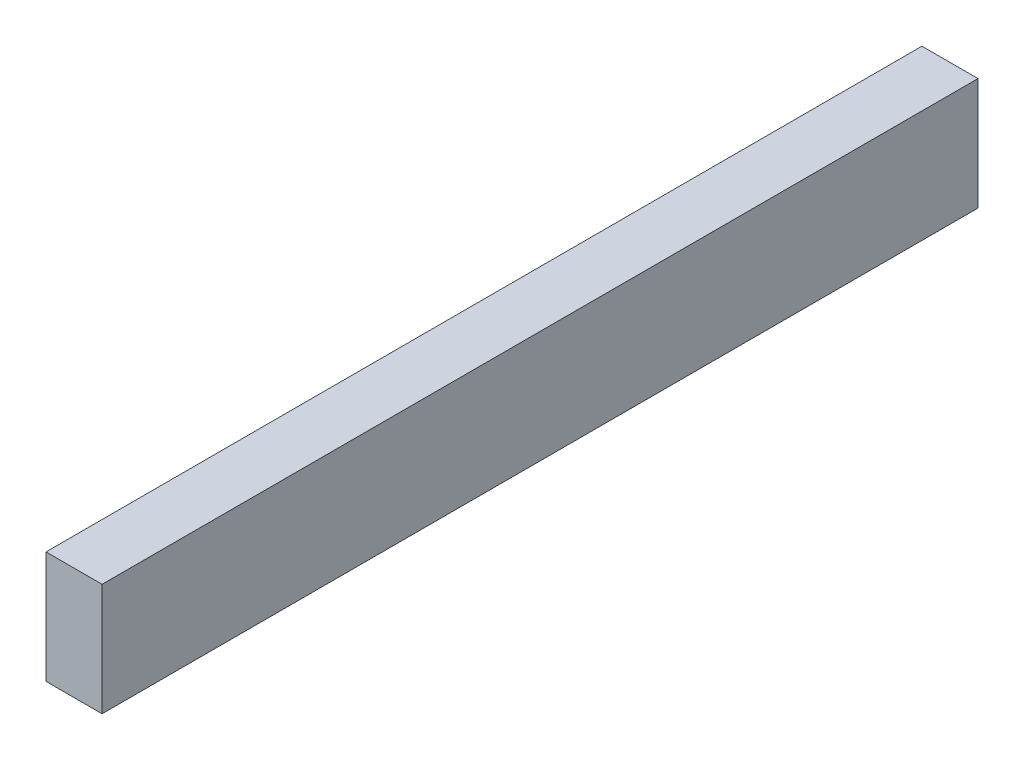
SolidWorks part; units mm, degrees
material "Cedar"
ref_plane "Front Plane" through (0, 0, 0) normal (0, 0, 1) x (1, 0, 0)
ref_plane "Top Plane" through (0, 0, 0) normal (0, 1, 0) x (1, 0, 0)
ref_plane "Right Plane" through (0, 0, 0) normal (1, 0, 0) x (0, 0, -1)
sketch "Sketch1" plane through (0, 0, 0) normal (1, 0, 0) x (0, 0, -1)
  line L1 (-119.1459, -37.5211) -> (178.3897, -37.5211)
  line L2 (-119.1459, -37.5211) -> (-119.1459, 0.5789)
  line L3 (-119.1459, 0.5789) -> (178.3897, 0.5789)
  line L4 (178.3897, -37.5211) -> (178.3897, 0.5789)
  dimension "D1" = 297.5356
  dimension "D2" = 38.1
extrude "Boss-Extrude1" add sketch "Sketch1" along normal blind 19.05
